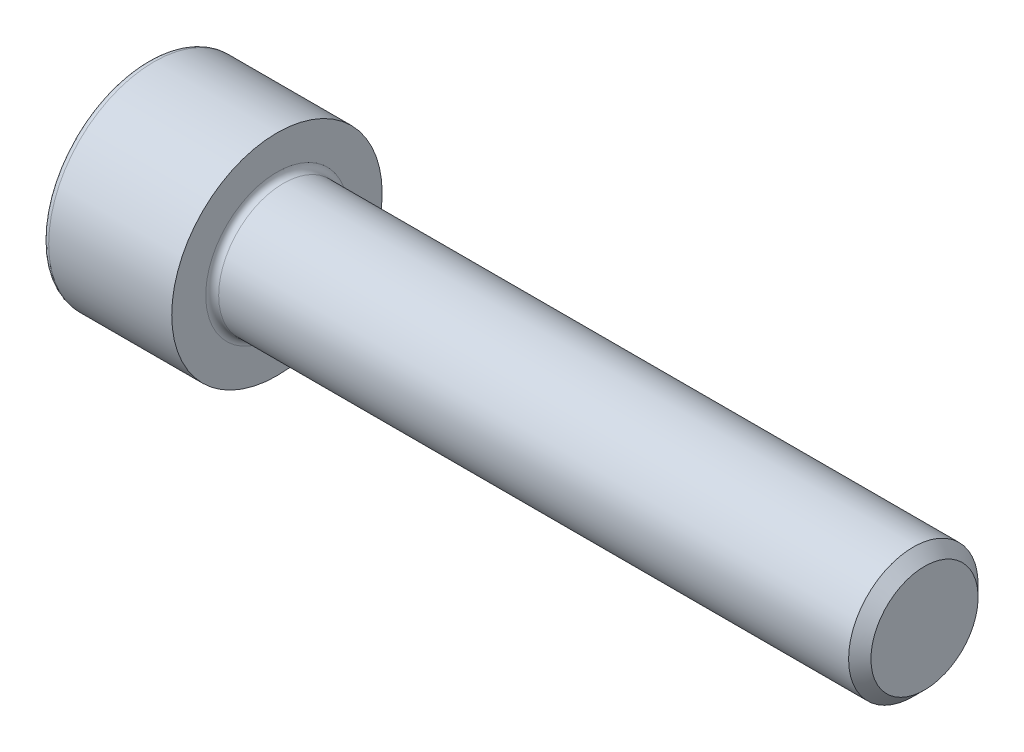
SolidWorks part; units mm, degrees
revolve "Base-Revolve" add sketch "BodySke"
sketch "BodySke" plane through (0, 0, 0) normal (0, 0, 1) x (1, 0, 0)
  line L0 (0, 0) -> (0, 6.5)
  line L1 (0, 6.5) -> (8, 6.5)
  line L2 (8, 6.5) -> (8, 4)
  line L3 (8, 4) -> (47.3095, 4)
  line L4 (48, 3.3095) -> (48, 0)
  line L5 (48, 0) -> (0, 0)
  line L6 (-31.75, 0) -> (127, 0) construction
  line L8 (48, 3.3095) -> (47.3095, 4)
  line L10 (48, -3.3095) -> (47.3095, -4) construction
  line L11 (9.25, 9.525) -> (9.25, 3.175) construction
  line L12 (20, 9.525) -> (20, 3.175) construction
  line L13 (-12, 9.525) -> (-12, 3.175) construction
  dimension "Head_ht" = 8
  dimension "Length" = 40
  dimension "Body_ch_ang" = 45
  dimension "Diameter" = 8
  dimension "Minor_dia" = 6.619
  dimension "Advance" = 1.25
  dimension "Thread_nom" = 28
  dimension "Thread_length" = 60
  dimension "Head_dia" = 13
cosmetic thread "ThreadCosmetic" [suppressed]
fillet "Fillet1" radius 0.4 1 edges at (8, 0, 4)
fillet "Fillet2" radius 0.4 1 edges at (0, 0, 6.5)
ref_plane "Plane1" through (0, 0, 0) normal (0, 0, 1) x (1, 0, 0)
ref_plane "Plane2" through (0, 0, 0) normal (0, 1, 0) x (1, 0, 0)
ref_plane "Plane3" through (0, 0, 0) normal (1, 0, 0) x (0, 0, -1)
sketch "Sketch2" plane through (0, 0, 0) normal (0, 0, 1) x (1, 0, 0)
  line L0 (0, 3.0475) -> (4, 3.0475)
  line L1 (4, 3.0475) -> (5.7595, 0)
  line L2 (-31.75, 0) -> (127, 0) construction
  line L3 (5.7595, 0) -> (0, 0)
  line L4 (0, 0) -> (0, 3.0475)
  line L6 (0, 0) -> (47.625, 0) construction
  dimension "D1" = 3.0475
  dimension "D2" = 60
  dimension "Depth" = 4
revolve "Hex-PreBroach" cut sketch "Sketch2" angle 360 about L6
sketch "Sketch3" plane through (0, 0, 0) normal (-1, 0, 0) x (0, 0.5, 0.866)
  line L0 (1.7595, 3.0475) -> (-1.7595, 3.0475)
  line L1 (-1.7595, 3.0475) -> (-3.5189, 0)
  line L2 (1.7595, 3.0475) -> (3.5189, 0)
  line L3 (1.7595, -3.0475) -> (3.5189, 0)
  line L4 (1.7595, -3.0475) -> (-1.7595, -3.0475)
  line L5 (-1.7595, -3.0475) -> (-3.5189, 0)
  dimension "D1" = 3.0475
  dimension "D2" = 3.0475
  dimension "Hex_size" = 6.095
extrude "Hex" cut sketch "Sketch3" against normal blind 4
sketch "ThdSchSke" plane through (0, 0, 0) normal (0, 0, 1) x (1, 0, 0)
  line L0 (20, -3.3095) -> (19.5165, -4)
  line L1 (20, -3.3095) -> (20.4835, -4)
  line L2 (20.4835, -4) -> (20.4835, -5)
  line L3 (-3.175, 0) -> (5.1513, 0) construction
  line L4 (0, 6.1) -> (0, -6.1) construction
  line L5 (20.4835, -5) -> (19.5165, -5)
  line L6 (19.5165, -5) -> (19.5165, -4)
  dimension "Thread_minor" = 6.619
  dimension "Diameter" = 8
  dimension "Start" = 20
revolve "ThreadSchematic" [suppressed] cut sketch "ThdSchSke" angle 360 about L3
pattern_linear "ThdSchPat" [suppressed]
equation "\"D2@Sketch3\" = \"Hex_size@Sketch3\" / 2"
equation "\"D1@Sketch3\" = \"Hex_size@Sketch3\" / 2"
equation "\"D1@Sketch2\" = \"Hex_size@Sketch3\" / 2"
equation "\"Thread_minor@ThreadCosmetic\"  =  \"Minor_dia@BodySke\""
equation "\"Depth@Sketch2\" =  \"Key_eng@Hex\""
equation "\"Thread_length@ThreadCosmetic\" = ((sgn( (\"Length@BodySke\" - \"Advance@BodySke\" * 3.0) - \"Thread_nom@BodySke\" )-1)*( (\"Length@BodySke\" - \"Advance@BodySke\" * 3.0) - \"Thread_nom@BodySke\" ))/-2+ \"Thread_nom@BodySke\""
equation "\"Thread_minor@ThdSchSke\" = \"Minor_dia@BodySke\""
equation "\"Diameter@ThdSchSke\" = \"Diameter@BodySke\""
equation "\"Overcut@ThdSchSke\" = \"Diameter@BodySke\" * 1.25"
equation "\"Start@ThdSchSke\" = \"Head_ht@BodySke\" + \"Length@BodySke\" - \"Thread_length@ThreadCosmetic\"  '---Non-countersunk---"
equation "\"Num_threads@ThdSchPat\" = int( \"Thread_length@ThreadCosmetic\" / \"Advance@BodySke\" + 0.999 )  + 1"
equation "\"Advance@ThdSchPat\" = \"Thread_length@ThreadCosmetic\" /  (\"Num_threads@ThdSchPat\" - 1) 'relax it"
equation "\"Num_threads@ThdSchPat\" = \"Num_threads@ThdSchPat\" - sgn( \"Num_threads@ThdSchPat\" - 1) '---chamfered tips only---"
